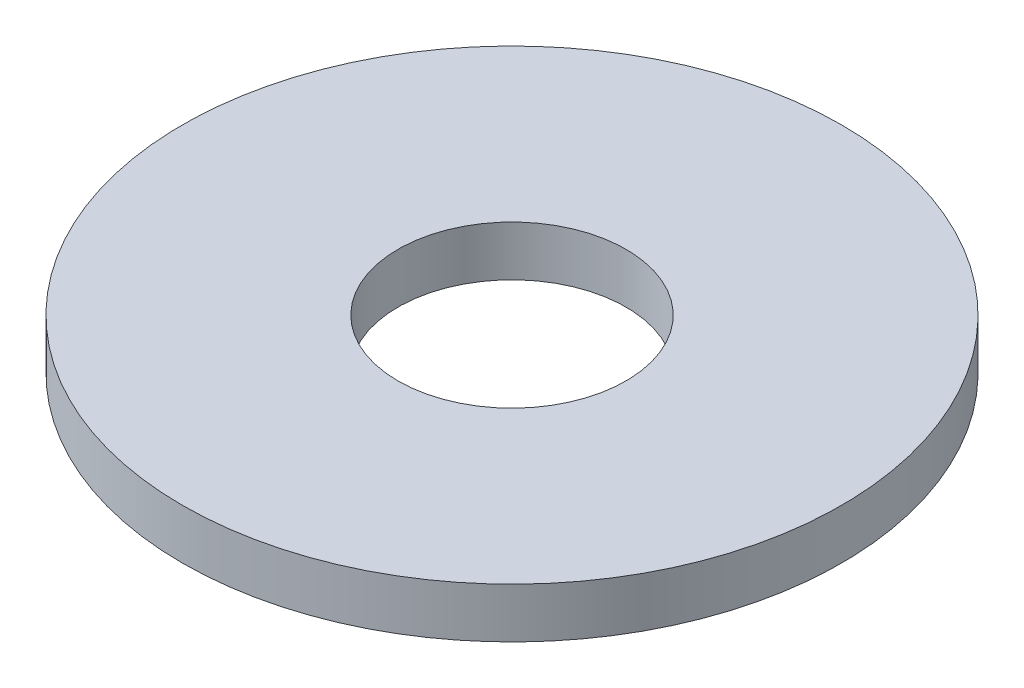
SolidWorks part; units mm, degrees
ref_plane "Спереди" through (0, 0, 0) normal (0, 0, 1) x (1, 0, 0)
ref_plane "Сверху" through (0, 0, 0) normal (0, 1, 0) x (1, 0, 0)
ref_plane "Справа" through (0, 0, 0) normal (1, 0, 0) x (0, 0, -1)
sketch "Sketch1" plane through (0, 0, 0) normal (0, 1, 0) x (1, 0, 0)
  circle A0 centre (0, 0) radius 11.85
  circle A1 centre (0, 0) radius 4.1
  dimension "D1" = 23.7
  dimension "D2" = 8.2
extrude "Boss-Extrude1" add sketch "Sketch1" along normal blind 1.8
